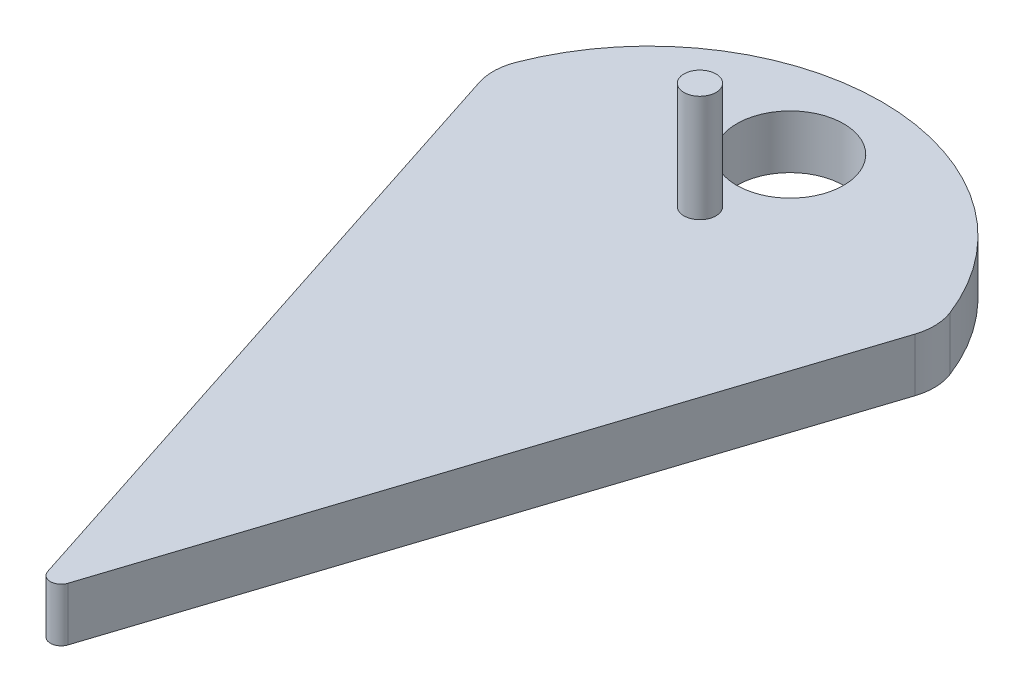
SolidWorks part; units mm, degrees
ref_plane "Front Plane" through (0, 0, 0) normal (0, 0, 1) x (1, 0, 0)
ref_plane "Top Plane" through (0, 0, 0) normal (0, 1, 0) x (1, 0, 0)
ref_plane "Right Plane" through (0, 0, 0) normal (1, 0, 0) x (0, 0, -1)
sketch "Sketch4" plane through (0, 0, 0) normal (0, 1, 0) x (1, 0, 0)
  line L0 (0, 0) -> (0, 80) construction
  line L1 (0.9511, 2.9271) -> (20.3862, 62.7423)
  line L2 (-0.9511, 2.9271) -> (-20.3862, 62.7423)
  circle A0 centre (0, 0) radius 80 construction
  arc A1 (-20.2941, 66.0915) -> (20.2941, 66.0915) centre (0, 58.24) cw
  arc A2 (-0.9511, 2.9271) -> (0.9511, 2.9271) centre (0, 3.2361) ccw
  arc A3 (20.3862, 62.7423) -> (20.2941, 66.0915) centre (15.6309, 64.2874) ccw
  arc A4 (-20.3862, 62.7423) -> (-20.2941, 66.0915) centre (-15.6309, 64.2874) cw
  circle A5 centre (0, 71.439) radius 5
  point P13 (20.8959, 64.3111)
  point P16 (-20.8959, 64.3111)
  dimension "D1" = 160
  dimension "D3" = 1
  dimension "D4" = 5
  dimension "D6" = 10
  dimension "D7" = 21.76
  dimension "D2" = 36
  dimension "D5" = 71.439
extrude "Boss-Extrude1" add sketch "Sketch4" along normal blind 5
sketch "Sketch7" plane through (0, 5, 0) normal (0, 1, 0) x (1, 0, 0)
  line L0 (0, 71.439) -> (6.6328, 71.439) construction
  circle A0 centre (0, 62.999) radius 1.5
  dimension "D2" = 3
  dimension "D1" = 8.44
extrude "Boss-Extrude2" add sketch "Sketch7" along normal blind 10
